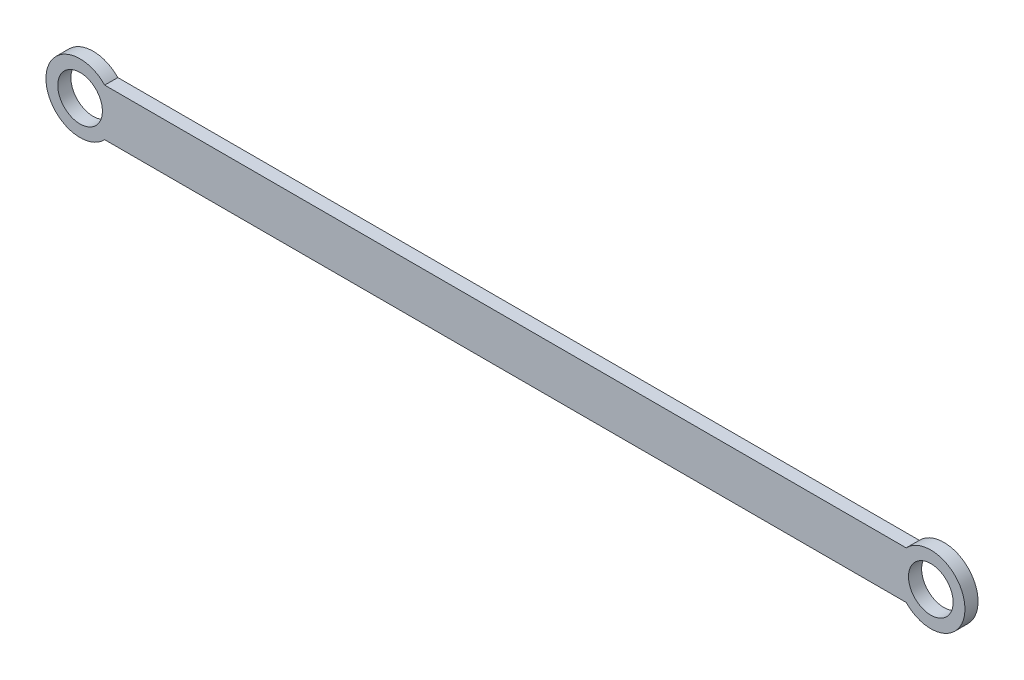
SolidWorks part; units mm, degrees
ref_plane "前视基准面" through (0, 0, 0) normal (0, 0, 1) x (1, 0, 0)
ref_plane "上视基准面" through (0, 0, 0) normal (0, 1, 0) x (1, 0, 0)
ref_plane "右视基准面" through (0, 0, 0) normal (1, 0, 0) x (0, 0, -1)
sketch "草图1" plane through (0, 0, 0) normal (0, 0, 1) x (1, 0, 0)
  line L0 (0, 0) -> (36.4097, 0) construction
  line L1 (36.4097, 0) -> (162, 0) construction
  line L2 (4.6904, 4.5) -> (157.3096, 4.5)
  line L3 (4.6904, -4.5) -> (157.3096, -4.5)
  circle A0 centre (0, 0) radius 4.25
  circle A1 centre (162, 0) radius 4.25
  arc A2 (4.6904, 4.5) -> (4.6904, -4.5) centre (0, 0) ccw
  arc A3 (157.3096, -4.5) -> (157.3096, 4.5) centre (162, 0) ccw
  dimension "D1" = 8.5
  dimension "D2" = 8.5
  dimension "D4" = 13
  dimension "D5" = 4.5
  dimension "13" = 13
  dimension "D3" = 162
extrude "凸台-拉伸1" add sketch "草图1" along normal blind 2.5
